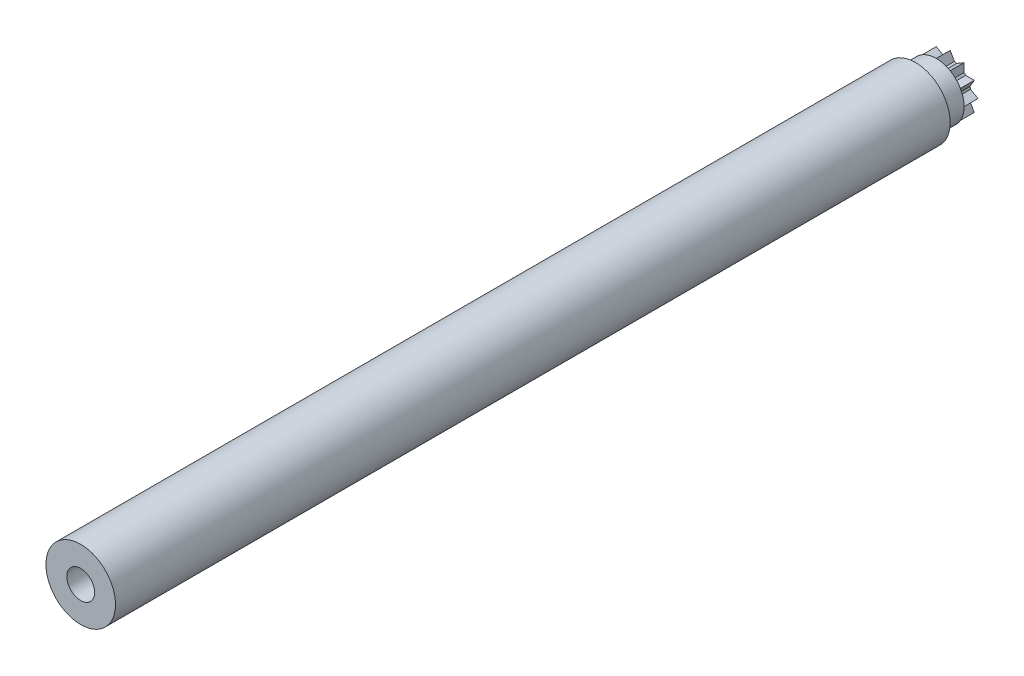
SolidWorks part; units mm, degrees
ref_plane "Ön Düzlem" through (0, 0, 0) normal (0, 0, 1) x (1, 0, 0)
ref_plane "Üst Düzlem" through (0, 0, 0) normal (0, 1, 0) x (1, 0, 0)
ref_plane "Sağ Düzlem" through (0, 0, 0) normal (1, 0, 0) x (0, 0, -1)
sketch "Çizim1" plane through (0, 0, 0) normal (0, 0, 1) x (1, 0, 0)
  circle A0 centre (0, 0) radius 2.5
  dimension "D1" = 5
extrude "Yükseklik-Ekstrüzyon1" add sketch "Çizim1" along normal blind 60
sketch "Çizim2" plane through (0, 0, 0) normal (0, 0, 1) x (1, 0, 0)
  circle A0 centre (0, 0) radius 2
  dimension "D1" = 4
extrude "Yükseklik-Ekstrüzyon2" add sketch "Çizim2" against normal blind 2.5
sketch "Çizim4" plane through (0, 0, -2.5) normal (0, 0, -1) x (-1, 0, 0)
  line L28 (-1.7321, 1) -> (-1.4241, 0.4666)
  line L29 (-2, 0) -> (-1.4666, 0.308)
  line L30 (-2, 0) -> (-1.4666, -0.308)
  line L31 (-1.7321, 1) -> (-1.1161, 1)
  line L32 (-1, 1.7321) -> (-1, 1.1161)
  line L33 (-1, 1.7321) -> (-0.4666, 1.4241)
  line L34 (0, 2) -> (-0.308, 1.4666)
  line L35 (0, 2) -> (0.308, 1.4666)
  line L36 (1, 1.7321) -> (0.4666, 1.4241)
  line L37 (1, 1.7321) -> (1, 1.1161)
  line L38 (1.7321, 1) -> (1.1161, 1)
  line L39 (1.7321, 1) -> (1.4241, 0.4666)
  line L40 (2, 0) -> (1.4666, 0.308)
  line L41 (2, 0) -> (1.4666, -0.308)
  line L42 (1.7321, -1) -> (1.4241, -0.4666)
  line L43 (1.7321, -1) -> (1.1161, -1)
  line L44 (1, -1.7321) -> (1, -1.1161)
  line L45 (1, -1.7321) -> (0.4666, -1.4241)
  line L46 (0, -2) -> (0.308, -1.4666)
  line L47 (0, -2) -> (-0.308, -1.4666)
  line L48 (-1, -1.7321) -> (-0.4666, -1.4241)
  line L49 (-1, -1.7321) -> (-1, -1.1161)
  line L50 (-1.7321, -1) -> (-1.1161, -1)
  line L51 (-1.7321, -1) -> (-1.4241, -0.4666)
  circle A1 centre (0, 0) radius 2 construction
  circle A18 centre (0, 0) radius 2
  circle A19 centre (0, 0) radius 2
  arc A31 (-1.4666, -0.308) -> (-1.4241, -0.4666) centre (0, 0) ccw
  arc A32 (-1.1161, -1) -> (-1, -1.1161) centre (0, 0) ccw
  arc A33 (-0.4666, -1.4241) -> (-0.308, -1.4666) centre (0, 0) ccw
  arc A34 (0.308, -1.4666) -> (0.4666, -1.4241) centre (0, 0) ccw
  arc A35 (1, -1.1161) -> (1.1161, -1) centre (0, 0) ccw
  arc A36 (1.4241, -0.4666) -> (1.4666, -0.308) centre (0, 0) ccw
  arc A37 (1.4666, 0.308) -> (1.4241, 0.4666) centre (0, 0) ccw
  arc A38 (1.1161, 1) -> (1, 1.1161) centre (0, 0) ccw
  arc A39 (0.4666, 1.4241) -> (0.308, 1.4666) centre (0, 0) ccw
  arc A40 (-0.308, 1.4666) -> (-0.4666, 1.4241) centre (0, 0) ccw
  arc A41 (-1, 1.1161) -> (-1.1161, 1) centre (0, 0) ccw
  arc A42 (-1.4241, 0.4666) -> (-1.4666, 0.308) centre (0, 0) ccw
  point P22 (0, 0)
  point P71 (0, 0)
  circle M19 centre (0, 0) radius 2
  dimension "D3" = 12
  dimension "D1" = 0
extrude "Kes-Ekstrüzyon1" cut sketch "Çizim4" against normal blind 1 contours A32 L50 L49 M19 | A33 L48 L47 M19 | A34 L46 L45 M19 | A35 L44 L43 M19 | A36 L42 L41 M19 | A37 L40 L39 M19 | A38 L38 L37 M19 | A39 L36 L35 M19 | A40 L34 L33 M19 | A41 L32 L31 M19 | A42 L28 L29 M19 | A31 L30 L51 M19
sketch "Çizim5" plane through (0, 0, -2.5) normal (0, 0, -1) x (-1, 0, 0)
  circle A0 centre (0, 0) radius 1
  dimension "D1" = 2
extrude "Kes-Ekstrüzyon2" cut sketch "Çizim5" against normal blind 71
